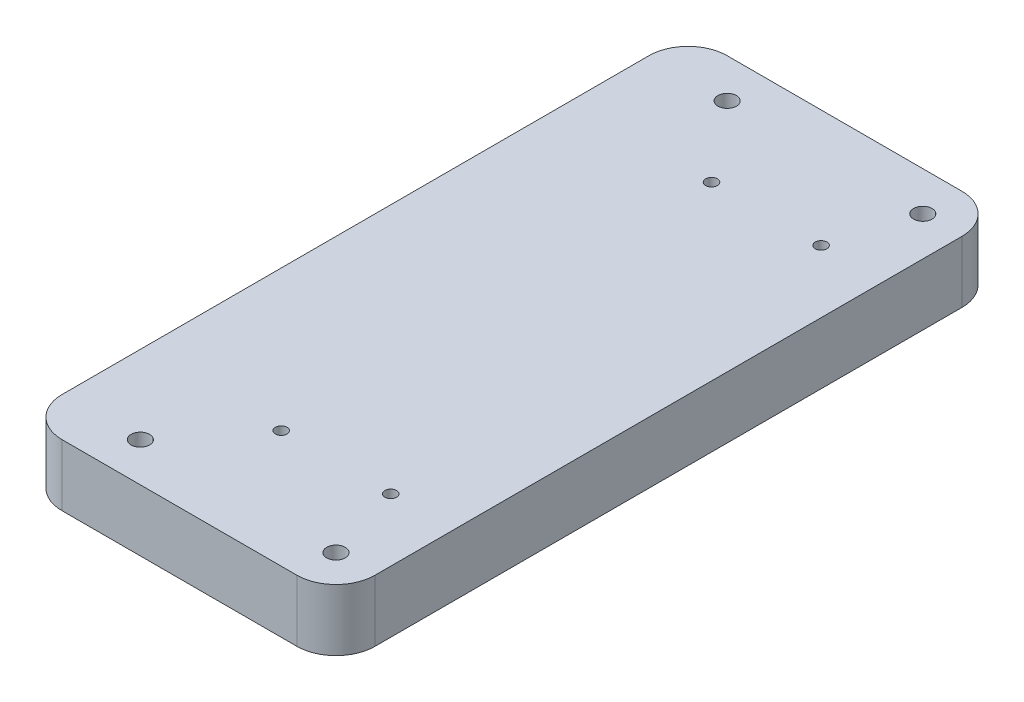
SolidWorks part; units mm, degrees
ref_plane "Front Plane" through (0, 0, 0) normal (0, 0, 1) x (1, 0, 0)
ref_plane "Top Plane" through (0, 0, 0) normal (0, 1, 0) x (1, 0, 0)
ref_plane "Right Plane" through (0, 0, 0) normal (1, 0, 0) x (0, 0, -1)
sketch "Sketch1" plane through (0, 0, 0) normal (0, 1, 0) x (1, 0, 0)
  line L1 (0, 0) -> (101.6, 0)
  line L2 (0, 0) -> (0, 215.9)
  line L3 (0, 215.9) -> (101.6, 215.9)
  line L4 (101.6, 0) -> (101.6, 215.9)
  dimension "9" = 215.9
  dimension "5.5" = 101.6
extrude "Boss-Extrude2" add sketch "Sketch1" along normal blind 20
sketch "Sketch4" plane through (0, 20, -20) normal (0, -1, 0) x (1, 0, 0)
  line L0 (101.6, -277.6562) -> (-114.3, -277.6563) construction
  line L1 (101.6, -246.7) -> (-114.3, -246.7) construction
  line L2 (101.6, -297.5) -> (-114.3, -297.5)
  line L3 (101.6, -297.5) -> (101.6, -195.9)
  line L4 (101.6, -195.9) -> (-114.3, -195.9)
  line L5 (-114.3, -297.5) -> (-114.3, -195.9)
  line L7 (0, 20) -> (101.6, 20) construction
  line L9 (0, -195.9) -> (0, 20) construction
  circle A0 centre (70.6438, -277.6562) radius 3.1
  circle A1 centre (-108.7437, -277.6563) radius 3.1
  circle A2 centre (70.6437, -215.7437) radius 3.1
  circle A3 centre (-108.7437, -215.7437) radius 3.1
  dimension "D2" = 6.2
  dimension "D3" = 30.9562
  dimension "D1" = 30.9562
  dimension "D4" = 2
fillet "Fillet1" radius 12.7 4 edges at (0, 10, -215.9) (101.6, 10, 0) (0, 10, 0) (101.6, 10, -215.9)
sketch "Sketch5" plane through (0, 0, 0) normal (0, -1, 0) x (-1, 0, 0)
  line L0 (-88.9, 215.9) -> (-12.7, 215.9) construction
  line L1 (-101.6, 12.7) -> (-101.6, 203.2) construction
  circle A0 centre (-88.9, 203.2) radius 3
  circle A1 centre (-25.4, 203.2) radius 3
  circle A2 centre (-88.9, 12.7) radius 3
  circle A3 centre (-25.4, 12.7) radius 3
  dimension "D3" = 6
  dimension "D1" = 12.7
  dimension "D2" = 12.7
  dimension "D4" = 12.7
  dimension "D5" = 63.5
  dimension "D6" = 190.5
  dimension "D7" = 63.5
  dimension "D8" = 190.5
  dimension "D9" = 12.7
extrude "Cut-Extrude1" cut sketch "Sketch5" against normal through all
sketch "Sketch7" plane through (0, 20, 0) normal (0, 1, 0) x (1, 0, 0)
  circle A1 centre (81.28, 177.8) radius 1.905
  circle A2 centre (81.28, 177.8) radius 1.905
  circle A3 centre (45.72, 177.8) radius 1.905
  circle A4 centre (45.72, 177.8) radius 1.905
  circle A5 centre (45.72, 38.1) radius 1.905
  circle A6 centre (45.72, 38.1) radius 1.905
  circle A7 centre (81.28, 38.1) radius 1.905
  circle A8 centre (81.28, 38.1) radius 1.905
  dimension "D1" = 0
  dimension "D2" = 0
  dimension "D3" = 0
  dimension "D4" = 0
extrude "Cut-Extrude2" cut sketch "Sketch7" against normal through all
equation "\"2c\"=0.787402"
